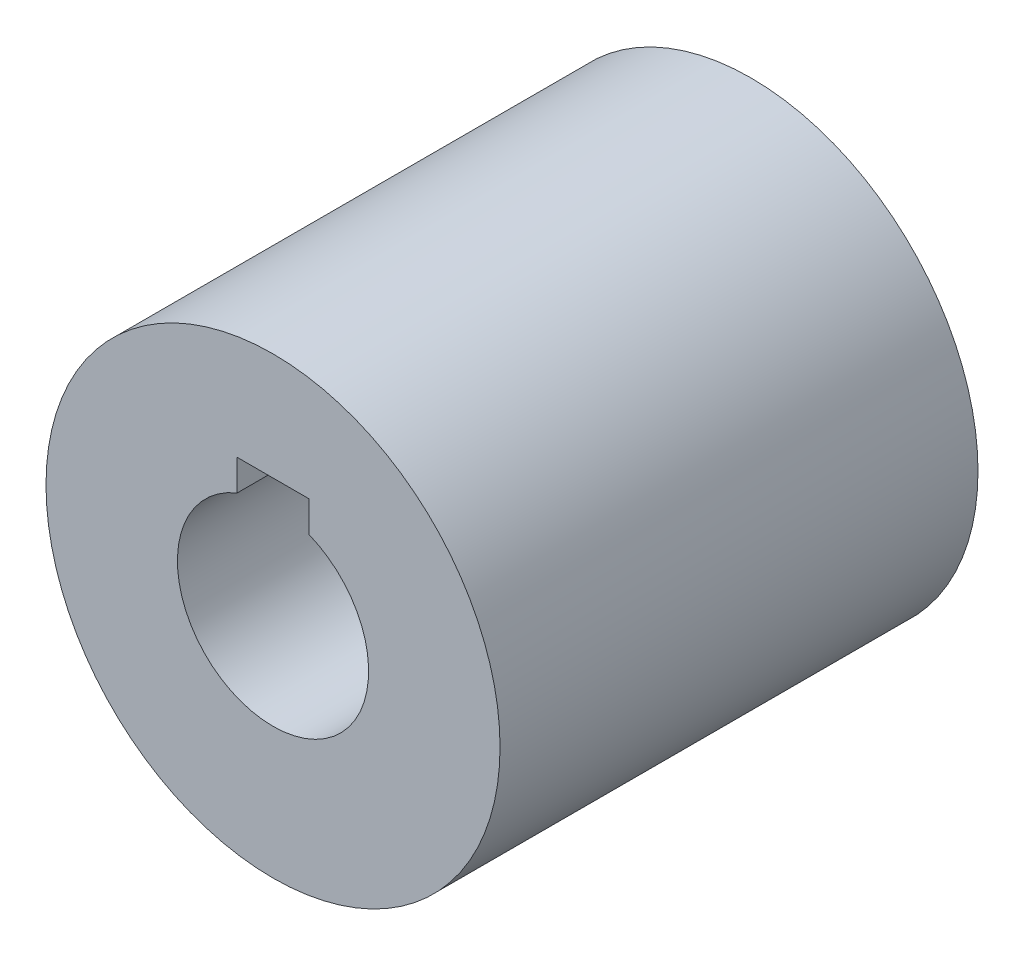
SolidWorks part; units mm, degrees
ref_plane "Front Plane" through (0, 0, 0) normal (0, 0, 1) x (1, 0, 0)
ref_plane "Top Plane" through (0, 0, 0) normal (0, 1, 0) x (1, 0, 0)
ref_plane "Right Plane" through (0, 0, 0) normal (1, 0, 0) x (0, 0, -1)
sketch "Sketch1" plane through (0, 0, 0) normal (0, 0, 1) x (1, 0, 0)
  line L0 (-1.5, 3.7081) -> (-1.5, 5)
  line L1 (-1.5, 5) -> (1.5, 5)
  line L2 (1.5, 5) -> (1.5, 3.7081)
  circle A0 centre (0, 0) radius 9.5
  arc A1 (-1.5, 3.7081) -> (1.5, 3.7081) centre (0, 0) ccw
  point P6 (0, 5)
  dimension "D1" = 19
  dimension "D2" = 8
  dimension "D3" = 5
  dimension "D4" = 3
extrude "Boss-Extrude1" add sketch "Sketch1" along normal blind 20
